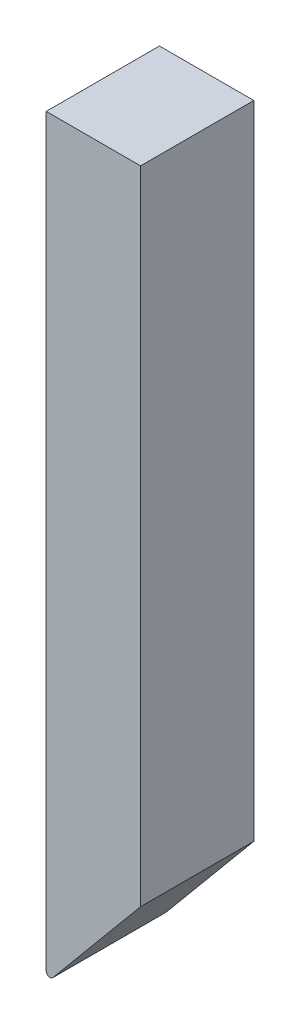
SolidWorks part; units mm, degrees
ref_plane "Front Plane" through (0, 0, 0) normal (0, 0, 1) x (1, 0, 0)
ref_plane "Top Plane" through (0, 0, 0) normal (0, 1, 0) x (1, 0, 0)
ref_plane "Right Plane" through (0, 0, 0) normal (1, 0, 0) x (0, 0, -1)
sketch "Sketch1" plane through (0, 0, 0) normal (0, 0, 1) x (1, 0, 0)
  line L0 (-1.25, -12.5) -> (1.25, -9.5)
  line L1 (-1.25, 7.5) -> (1.25, 7.5)
  line L2 (-1.25, 7.5) -> (-1.25, -12.5)
  line L4 (1.25, 7.5) -> (1.25, -9.5)
  point P0 (0, 0)
  dimension "D1" = 2.5
  dimension "D2" = 20
  dimension "D3" = 17
extrude "Boss-Extrude1" add sketch "Sketch1" along normal blind 3
fillet "Fillet2" radius 0.1 1 edges at (-1.25, -12.5, 1.5)
